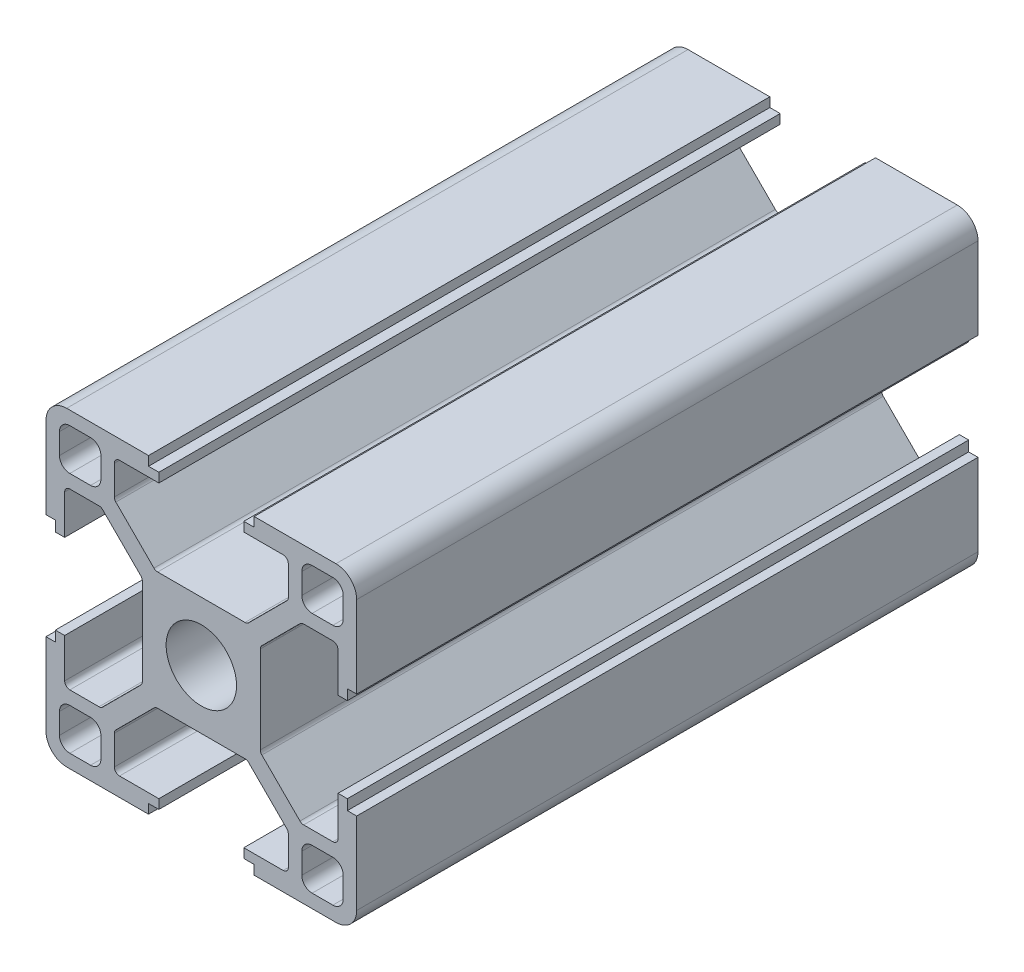
SolidWorks part; units mm, degrees
ref_plane "前视基准面" through (0, 0, 0) normal (0, 0, 1) x (1, 0, 0)
ref_plane "上视基准面" through (0, 0, 0) normal (0, 1, 0) x (1, 0, 0)
ref_plane "右视基准面" through (0, 0, 0) normal (1, 0, 0) x (0, 0, -1)
sketch "草图1" plane through (0, 0, 0) normal (0, 0, 1) x (1, 0, 0)
  line L0 (0, 0) -> (0, 65.3905) construction
  line L1 (0, 0) -> (64.2648, 0) construction
  line L2 (0, 0) -> (79.9729, 79.9729) construction
  line L3 (5.7, 0) -> (5.7, 4.4272)
  line L4 (5.7, 4.4272) -> (9.6728, 8.4)
  line L5 (9.6728, 8.4) -> (13.2, 8.4)
  line L6 (13.2, 8.4) -> (13.2, 4.1)
  line L7 (13.2, 4.1) -> (14.1, 4.1)
  line L8 (14.1, 4.1) -> (14.1, 5.1)
  line L9 (14.1, 5.1) -> (15, 5.1)
  line L10 (15, 5.1) -> (15, 15)
  line L11 (5.1, 15) -> (15, 15)
  line L12 (5.1, 14.1) -> (5.1, 15)
  line L13 (4.1, 14.1) -> (5.1, 14.1)
  line L14 (4.1, 13.2) -> (4.1, 14.1)
  line L15 (8.4, 13.2) -> (4.1, 13.2)
  line L16 (8.4, 9.6728) -> (8.4, 13.2)
  line L17 (4.4272, 5.7) -> (8.4, 9.6728)
  line L18 (0, 5.7) -> (4.4272, 5.7)
  line L20 (9.7, 9.7) -> (13.7, 9.7)
  line L21 (9.7, 9.7) -> (9.7, 13.7)
  line L22 (9.7, 13.7) -> (13.7, 13.7)
  line L23 (13.7, 9.7) -> (13.7, 13.7)
  line L24 (9.7, 9.7) -> (13.7, 13.7) construction
  line L25 (9.7, 13.7) -> (13.7, 9.7) construction
  line L26 (0, 5.7) -> (0, 0)
  line L27 (0, 0) -> (5.7, 0)
  point P9 (11.7, 11.7)
  dimension "D1" = 45
  dimension "D2" = 5.7
  dimension "D3" = 1.8
  dimension "D4" = 0.9
  dimension "D5" = 8.2
  dimension "D6" = 10.2
  dimension "D7" = 1.8
  dimension "D8" = 15
  dimension "D9" = 16.8
  dimension "D10" = 4
  dimension "D11" = 1.3
extrude "凸台-拉伸1" add sketch "草图1" along normal blind 60 contours L3 L4 L5 L6 L7 L8 L9 L10 L11 L12 L13 L14 L15 L16 L17 L18 L26 L27
fillet "圆角1" radius 1 4 edges at (9.7, 9.7, 30) (13.7, 9.7, 30) (9.7, 13.7, 30) (13.7, 13.7, 30)
fillet "圆角2" radius 2 1 edges at (15, 15, 30)
fillet "圆角3" radius 0.5 6 edges at (5.7, 4.4272, 30) (4.4272, 5.7, 30) (8.4, 13.2, 30) (8.4, 9.6728, 30) (9.6728, 8.4, 30) (13.2, 8.4, 30)
pattern_circular "阵列(圆周)1" count 4 over 360 about axis through (0, 0, 0) along (0, 0, 1) of "圆角2", "圆角3", "凸台-拉伸1", "圆角1"
sketch "草图2" plane through (0, 0, 60) normal (0, 0, 1) x (1, 0, 0)
  circle A0 centre (0, 0) radius 3.4
  dimension "D1" = 6.8
extrude "切除-拉伸1" cut sketch "草图2" against normal through all
sketch "草图3" plane through (0, 0, 0) normal (1, 0, 0) x (0, 0, -1)
  line L0 (-30, 60.2652) -> (-30, -70.1349) construction
  line L1 (-318.169, 0) -> (51.4974, 0) construction
  line L2 (0, 5.1) -> (0, 13) construction
  line L3 (-60, 5.1) -> (-60, 13) construction
  circle A1 centre (-45, 0) radius 3.15
  circle A2 centre (-15, 0) radius 3.15
  dimension "D1" = 6.3
  dimension "D2" = 30
extrude "切除-拉伸2" cut sketch "草图3" against normal mid plane 20
sketch "草图4" plane through (0, 5.7, 0) normal (0, 1, 0) x (1, 0, 0)
  line L0 (0, 8.1572) -> (0, -64.7671) construction
  line L1 (-28.4457, -30) -> (35.9868, -30) construction
  line L2 (-5.1, 0) -> (-13, 0) construction
  line L3 (-5.1, -60) -> (-13, -60) construction
  circle A0 centre (0, -30) radius 4.1
  dimension "D1" = 8.2
extrude "切除-拉伸3" cut sketch "草图4" against normal through all contours A0
